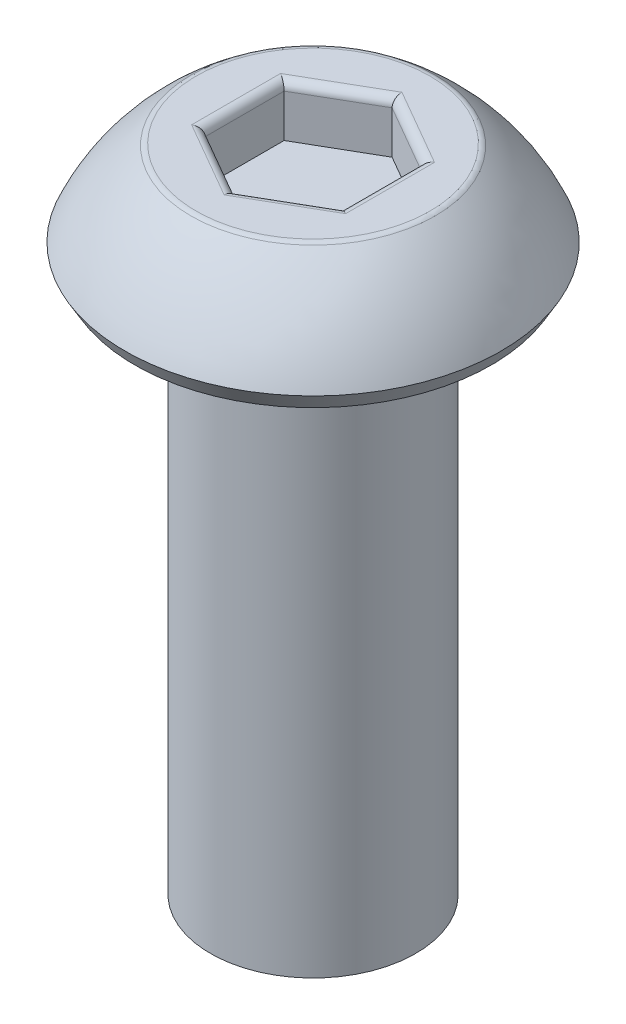
SolidWorks part; units mm, degrees
ref_plane "Front Plane" through (0, 0, 0) normal (0, 0, 1) x (1, 0, 0)
ref_plane "Top Plane" through (0, 0, 0) normal (0, 1, 0) x (1, 0, 0)
ref_plane "Right Plane" through (0, 0, 0) normal (1, 0, 0) x (0, 0, -1)
sketch "Sketch1" plane through (0, 0, 0) normal (1, 0, 0) x (0, 0, -1)
  line L0 (0, 0) -> (0, 1.5) construction
  line L1 (0, 1.5) -> (-1.75, 1.5)
  line L3 (-2.75, 0.25) -> (-2.6057, 0)
  line L4 (-2.6057, 0) -> (-1.5, 0)
  line L5 (-1.5, 0) -> (-1.5, -8)
  line L6 (-1.5, -8) -> (0, -8)
  line L7 (0, -8) -> (0, 1.5)
  line L8 (0, 0) -> (-1.5, 0) construction
  arc A0 (-1.75, 1.5) -> (-2.75, 0.25) centre (0.0077, -0.9312) ccw
  dimension "D5" = 3
  dimension "D1" = 1.5
  dimension "D2" = 2.75
  dimension "D3" = 1.75
  dimension "D4" = 0.25
  dimension "D6" = 60
  dimension "D7" = 1.5
  dimension "D8" = 8
revolve "Revolve1" add sketch "Sketch1" angle 360 about L7
sketch "Sketch2" plane through (0, 1.5, 0) normal (0, 1, 0) x (1, 0, 0)
  line L1 (0, 1.1547) -> (-1, 0.5774)
  line L2 (-1, 0.5774) -> (-1, -0.5774)
  line L3 (-1, -0.5774) -> (0, -1.1547)
  line L4 (0, -1.1547) -> (1, -0.5774)
  line L5 (1, -0.5774) -> (1, 0.5774)
  line L6 (1, 0.5774) -> (0, 1.1547)
  circle A0 centre (0, 0) radius 1 construction
  dimension "D1" = 2
extrude "Cut-Extrude1" cut sketch "Sketch2" against normal blind 0.75
fillet "Fillet1" radius 0.125 7 edges at (0, 1.5, -1.75) (-0.5, 1.5, 0.866) (0.5, 1.5, 0.866) (1, 1.5, 0) (0.5, 1.5, -0.866) (-0.5, 1.5, -0.866) (-1, 1.5, 0)
